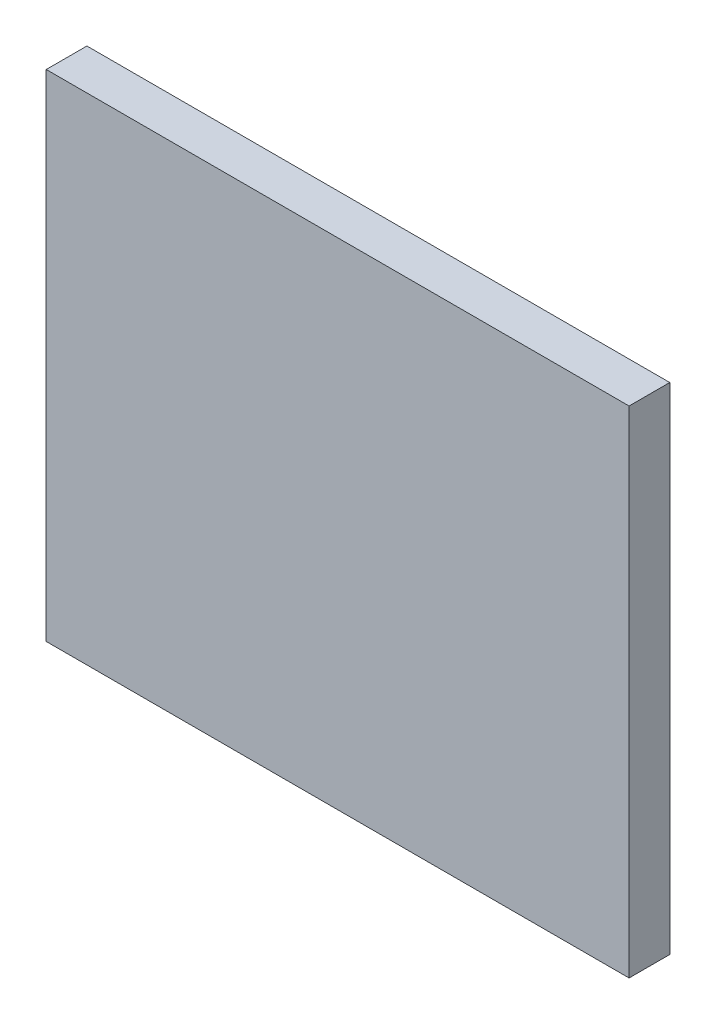
SolidWorks part; units mm, degrees
material "PET"
ref_plane "Plano frontal" through (0, 0, 0) normal (0, 0, 1) x (1, 0, 0)
ref_plane "Plano superior" through (0, 0, 0) normal (0, 1, 0) x (1, 0, 0)
ref_plane "Plano direito" through (0, 0, 0) normal (1, 0, 0) x (0, 0, -1)
sketch "Esboço1" plane through (0, 0, 0) normal (0, 0, 1) x (1, 0, 0)
  line L0 (39.98, 32.89) -> (39.98, -0.01) construction
  line L1 (0, 0) -> (39.98, 0)
  line L2 (0, 0) -> (0, 33.98)
  line L3 (0, 33.98) -> (39.98, 33.98)
  line L4 (39.98, 0) -> (39.98, 33.98)
  line L5 (38.99, 33.98) -> (0.99, 33.98) construction
extrude "Ressalto-extrusão1" add sketch "Esboço1" along normal blind 2.79
